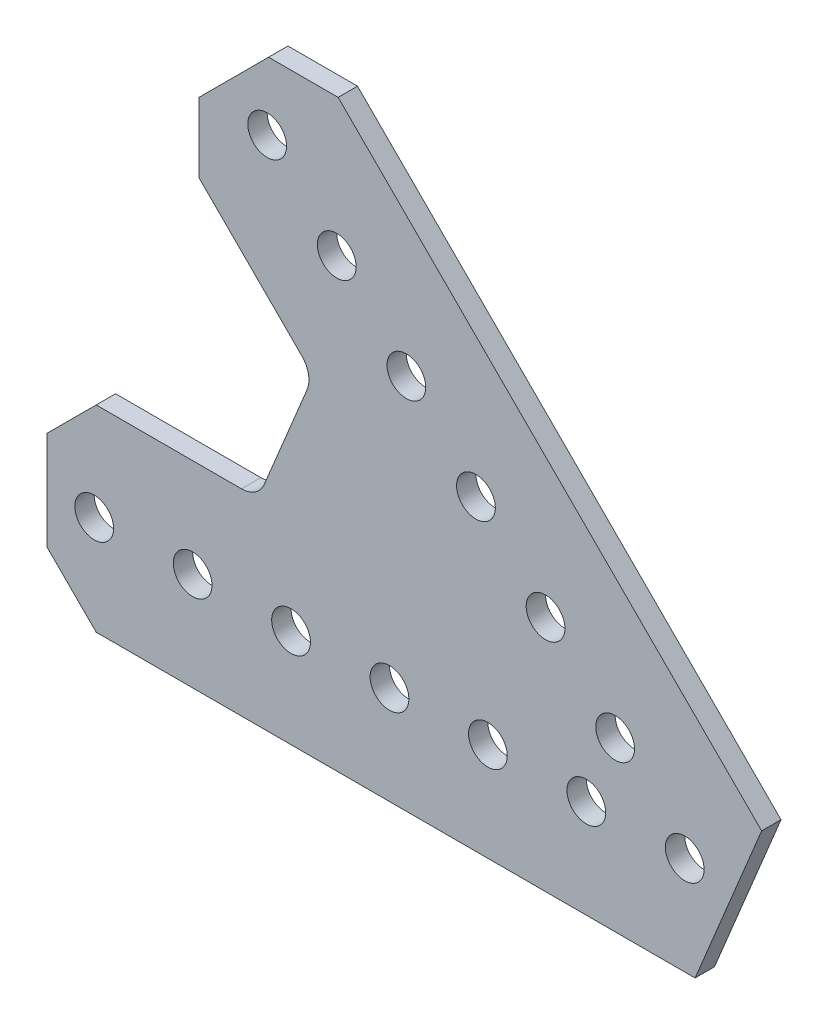
SolidWorks part; units mm, degrees
material "5052-H32"
ref_plane "Front Plane" through (0, 0, 0) normal (0, 0, 1) x (1, 0, 0)
ref_plane "Top Plane" through (0, 0, 0) normal (0, 1, 0) x (1, 0, 0)
ref_plane "Right Plane" through (0, 0, 0) normal (1, 0, 0) x (0, 0, -1)
ref_plane "Plane1" through (0, 0, -1.25) normal (0, 0, -1) x (-1, 0, 0)
sketch "Sketch1" plane through (0, 0, -1.25) normal (0, 0, -1) x (-1, 0, 0)
  line L0 (-1.3378, -12.7) -> (75.946, -12.7)
  line L1 (75.946, -12.7) -> (82.296, -6.35)
  line L2 (82.296, -6.35) -> (82.296, 6.35)
  line L3 (82.296, 6.35) -> (75.946, 12.7)
  line L4 (75.946, 12.7) -> (57.1932, 12.7)
  line L5 (54.2599, 14.66) -> (48.7337, 28.0014)
  line L6 (49.422, 31.4614) -> (62.6822, 44.7217)
  line L7 (62.6822, 44.7217) -> (62.6822, 53.7019)
  line L8 (62.6822, 53.7019) -> (53.7019, 62.6822)
  line L9 (53.7019, 62.6822) -> (44.7217, 62.6822)
  line L10 (44.7217, 62.6822) -> (-9.9262, 8.0343)
  line L11 (-9.9262, 8.0343) -> (-1.3378, -12.7)
  circle A0 centre (12.7, 0) radius 2.5
  circle A1 centre (25.4, 0) radius 2.5
  circle A2 centre (38.1, 0) radius 2.5
  circle A3 centre (50.8, 0) radius 2.5
  circle A4 centre (0, 0) radius 2.5
  circle A5 centre (76.2, 0) radius 2.5
  circle A6 centre (63.5, 0) radius 2.5
  circle A7 centre (53.8815, 53.8815) radius 2.5
  circle A8 centre (44.9013, 44.9013) radius 2.5
  circle A9 centre (35.921, 35.921) radius 2.5
  circle A10 centre (26.9408, 26.9408) radius 2.5
  circle A11 centre (17.9605, 17.9605) radius 2.5
  circle A12 centre (8.9803, 8.9803) radius 2.5
  arc A13 (57.1932, 12.7) -> (54.2599, 14.66) centre (57.1932, 15.875) cw
  arc A14 (48.7337, 28.0014) -> (49.422, 31.4614) centre (51.667, 29.2164) cw
extrude "Boss-Extrude1" add sketch "Sketch1" against normal blind 2.5
